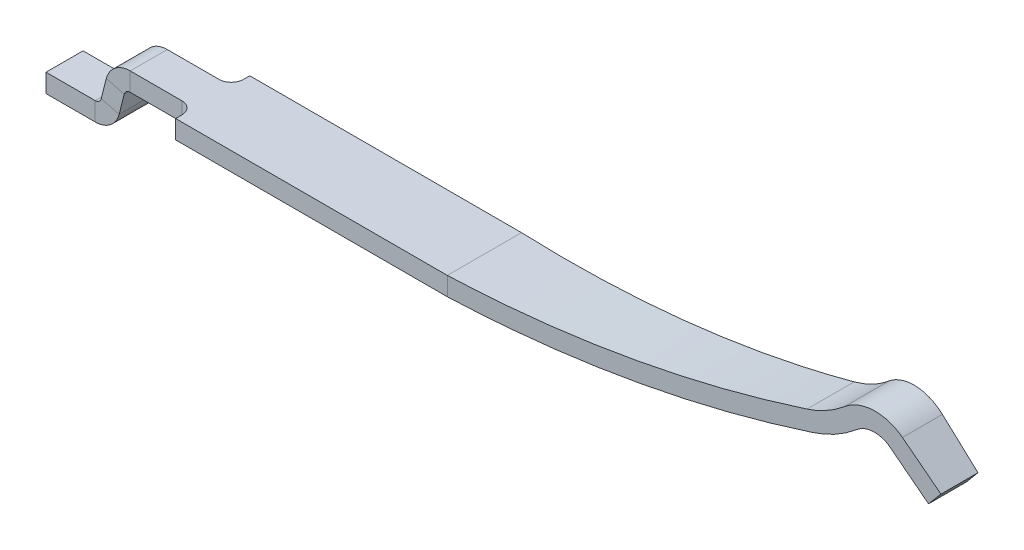
SolidWorks part; units mm, degrees
ref_plane "Front Plane" through (0, 0, 0) normal (0, 0, 1) x (1, 0, 0)
ref_plane "Top Plane" through (0, 0, 0) normal (0, 1, 0) x (1, 0, 0)
ref_plane "Right Plane" through (0, 0, 0) normal (1, 0, 0) x (0, 0, -1)
sketch "Sketch1" plane through (0, 0, 0) normal (1, 0, 0) x (0, 0, -1)
  line L1 (-0.3, 0.5) -> (0.3, 0.5)
  line L2 (-0.3, 0.5) -> (-0.3, 0.35)
  line L3 (-0.3, 0.35) -> (0.3, 0.35)
  line L4 (0.3, 0.5) -> (0.3, 0.35)
  line L5 (-0.3, 0.5) -> (0.3, 0.35) construction
  line L6 (-0.3, 0.35) -> (0.3, 0.5) construction
  point P0 (0, 0.425)
  dimension "D1" = 0.35
  dimension "D2" = 0.6
  dimension "D3" = 0.15
extrude "Boss-Extrude1" add sketch "Sketch1" along normal blind 1.7 contours L3 L4 L1 L2
sketch "Sketch2" plane through (0, 0, 0) normal (0, 1, 0) x (1, 0, 0)
  line L0 (0, 0) -> (-1.2, 0) construction
  dimension "D1" = 1.2
ref_plane "Plane1" through (-1.2, 0, 0) normal (1, 0, 0) x (0, 0, -1)
sketch "Sketch4" plane through (0, 0, 0) normal (0, 0, 1) x (1, 0, 0)
  line L0 (-1.2, 0) -> (-0.8017, 0)
  line L1 (0, 0) -> (-1.2, 0) construction
  line L2 (-1.2, -0.2475) -> (-1.2, 0.2475) construction
  line L3 (-0.5664, 0.3124) -> (-0.608, 0.1503)
  line L4 (-0.518, 0.35) -> (0, 0.35)
  arc A0 (-0.518, 0.35) -> (-0.5664, 0.3124) centre (-0.518, 0.3) ccw
  arc A1 (-0.608, 0.1503) -> (-0.8017, 0) centre (-0.8017, 0.2) cw
  dimension "D1" = 0.05
  dimension "D3" = 0.2
  dimension "D4" = 0.09
sketch "Sketch3" plane through (-1.2, 0, 0) normal (1, 0, 0) x (0, 0, -1)
  line L1 (0.15, 0.15) -> (-0.15, 0.15)
  line L2 (0.15, 0.15) -> (0.15, 0)
  line L3 (0.15, 0) -> (-0.15, 0)
  line L4 (-0.15, 0.15) -> (-0.15, 0)
  dimension "D1" = 0.3
  dimension "D2" = 0.15
sweep "Sweep1" add profiles "Sketch3" path "Sketch4"
fillet "Fillet1" radius 0.1 2 edges at (0, 0.425, -0.15) (0, 0.425, 0.15)
sketch "Sketch5" plane through (0, 0, 0) normal (0, 0, 1) x (1, 0, 0)
  line L0 (1.7, 0.35) -> (2.2, 0.35)
  line L1 (5.65, 0.9529) -> (5.95, 0.7)
  line L2 (-1.2, 0.15) -> (-1.2, 0) construction
  line L3 (0, 0) -> (5.95, 0) construction
  arc A0 (2.2, 0.35) -> (5.0464, 0.7661) centre (2.2, 10.294) ccw
  arc A1 (5.3922, 0.9529) -> (5.0464, 0.7661) centre (4.7702, 1.6907) cw
  arc A2 (5.3922, 0.9529) -> (5.65, 0.9529) centre (5.5211, 0.8) cw
  dimension "D5" = 0.2
  dimension "D1" = 7.15
  dimension "D2" = 0.3
  dimension "D3" = 0.5
  dimension "D4" = 1
  dimension "D8" = 0.7
sketch "Sketch6" plane through (1.7, 0, 0) normal (1, 0, 0) x (0, 0, -1)
  line L0 (-0.3, 0.5) -> (0.3, 0.5) construction
  line L1 (-0.3, 0.5) -> (-0.3, 0.35) construction
  line L2 (-0.3, 0.35) -> (0.3, 0.35) construction
  line L3 (0.3, 0.5) -> (0.3, 0.35) construction
  line L4 (-0.3, 0.5) -> (0.3, 0.5)
  line L5 (-0.3, 0.5) -> (-0.3, 0.35)
  line L6 (-0.3, 0.35) -> (0.3, 0.35)
  line L7 (0.3, 0.5) -> (0.3, 0.35)
sweep "Sweep2" add profiles "Sketch6" path "Sketch5"
sketch "Sketch8" plane through (0, 0, 0) normal (0, 1, 0) x (1, 0, 0)
  line L0 (-1.2, 0.4326) -> (6.0467, 0.15)
  line L1 (6.0467, 0.3) -> (6.0467, -0.3) construction
  line L2 (6.0467, 0.15) -> (6.0467, -0.15)
  line L3 (6.0467, -0.15) -> (-1.2, -0.4326)
  line L4 (-1.2, -0.4326) -> (-1.2, 0.4326)
  line L5 (-1.2, 0.15) -> (-1.2, -0.15) construction
  point P8 (6.0467, 0)
  dimension "D1" = 0.3
extrude "Cut-Extrude2" cut sketch "Sketch8" along normal through all flip side to cut
equation "\"pin_leg_start\"= 10.75"
equation "\"slot_offset\"= 2.6"
equation "\"pin_head_slot_offset\"= 1"
equation "\"pin_length\"= \"pin_leg_start\" - \"slot_offset\" - \"pin_head_slot_offset\""
equation "\"slot_length\"= 5.3"
equation "\"pin_leg_length\"= 1.2"
equation "\"D1@Sketch2\"=\"pin_leg_length\""
equation "\"D1@Sketch5\"=\"pin_length\""
